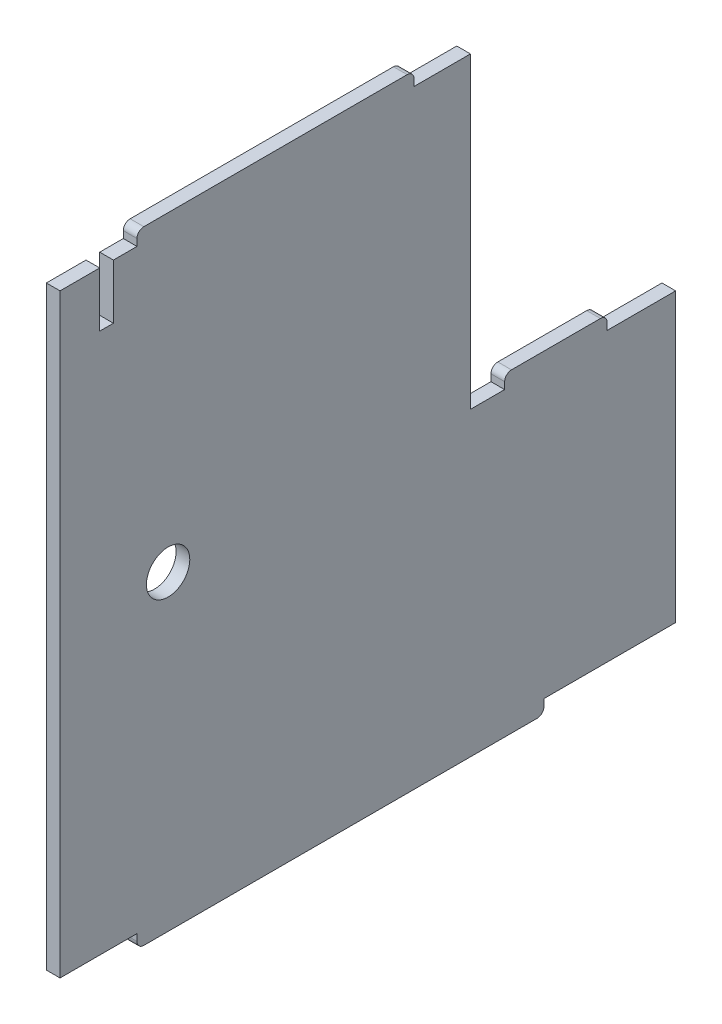
SolidWorks part; units mm, degrees
ref_plane "Front Plane" through (0, 0, 0) normal (0, 0, 1) x (1, 0, 0)
ref_plane "Top Plane" through (0, 0, 0) normal (0, 1, 0) x (1, 0, 0)
ref_plane "Right Plane" through (0, 0, 0) normal (1, 0, 0) x (0, 0, -1)
sketch "Sketch2" plane through (0, 0, 0) normal (1, 0, 0) x (0, 0, -1)
  line L1 (44.7524, -64.2438) -> (44.7524, -22.2438)
  line L2 (14.7524, -22.2438) -> (14.7524, 22.7562)
  line L3 (33.7524, -20.2438) -> (20.7524, -20.2438)
  line L4 (-33.9971, -64.2438) -> (-33.9971, -65.2438)
  line L5 (-37.4476, 22.7562) -> (-33.9971, 22.7562)
  line L6 (44.7524, -64.2438) -> (25.5019, -64.2438)
  line L7 (-45.2476, -64.2438) -> (-33.9971, -64.2438)
  line L8 (44.7524, -22.2438) -> (34.7524, -22.2438)
  line L9 (19.7524, -22.2438) -> (19.7524, -21.2438)
  line L10 (5.5019, 24.7562) -> (-32.9971, 24.7562)
  line L11 (25.5019, -64.2438) -> (25.5019, -65.2438)
  line L12 (34.7524, -22.2438) -> (34.7524, -21.2438)
  line L13 (19.7524, -22.2438) -> (14.7524, -22.2438)
  line L14 (6.5019, 22.7562) -> (14.7524, 22.7562)
  line L15 (-33.9971, 22.7562) -> (-33.9971, 23.7562)
  line L16 (-32.9971, -66.2438) -> (24.5019, -66.2438)
  line L17 (6.5019, 22.7562) -> (6.5019, 23.7562)
  line L18 (-45.2476, -64.2438) -> (-45.2476, 22.7562)
  line L19 (-37.4476, 14.7562) -> (-39.4476, 14.7562)
  line L20 (-37.4476, 14.7562) -> (-37.4476, 22.7562)
  line L21 (-39.4476, 22.7562) -> (-45.2476, 22.7562)
  line L22 (-39.4476, 14.7562) -> (-39.4476, 22.7562)
  arc A0 (-32.9971, -66.2438) -> (-33.9971, -65.2438) centre (-32.9971, -65.2438) cw
  arc A1 (34.7524, -21.2438) -> (33.7524, -20.2438) centre (33.7524, -21.2438) ccw
  arc A3 (19.7524, -21.2438) -> (20.7524, -20.2438) centre (20.7524, -21.2438) cw
  arc A4 (24.5019, -66.2438) -> (25.5019, -65.2438) centre (24.5019, -65.2438) ccw
  arc A5 (6.5019, 23.7562) -> (5.5019, 24.7562) centre (5.5019, 23.7562) ccw
  arc A6 (-33.9971, 23.7562) -> (-32.9971, 24.7562) centre (-32.9971, 23.7562) cw
  circle A11 centre (-29.4476, -20.7438) radius 3.17
extrude "Boss-Extrude1" add sketch "Sketch2" along normal blind 2
